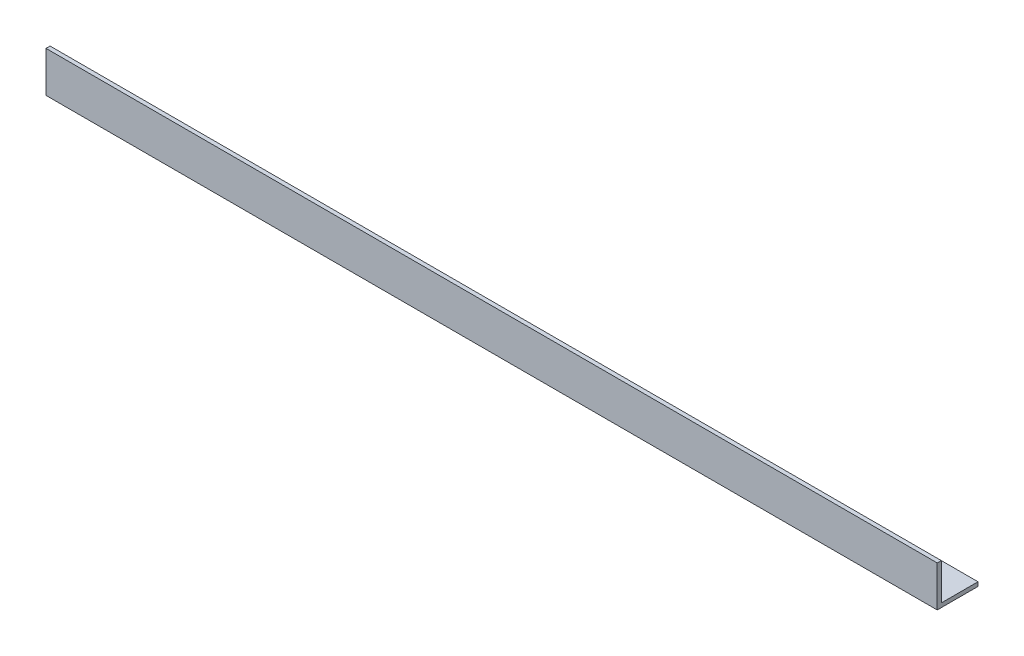
SolidWorks part; units mm, degrees
ref_plane "Спереди" through (0, 0, 0) normal (0, 0, 1) x (1, 0, 0)
ref_plane "Сверху" through (0, 0, 0) normal (0, 1, 0) x (1, 0, 0)
ref_plane "Справа" through (0, 0, 0) normal (1, 0, 0) x (0, 0, -1)
sketch "Эскиз1" plane through (0, 0, 0) normal (1, 0, 0) x (0, 0, -1)
  line L0 (0, 0) -> (0, 15)
  line L1 (0, 15) -> (1.5, 15)
  line L2 (1.5, 15) -> (1.5, 1.5)
  line L3 (1.5, 1.5) -> (15, 1.5)
  line L4 (15, 1.5) -> (15, 0)
  line L5 (15, 0) -> (0, 0)
  dimension "D1" = 15
  dimension "D2" = 15
  dimension "D3" = 1.5
  dimension "D4" = 1.5
extrude "Бобышка-Вытянуть1" add sketch "Эскиз1" along normal blind 328
